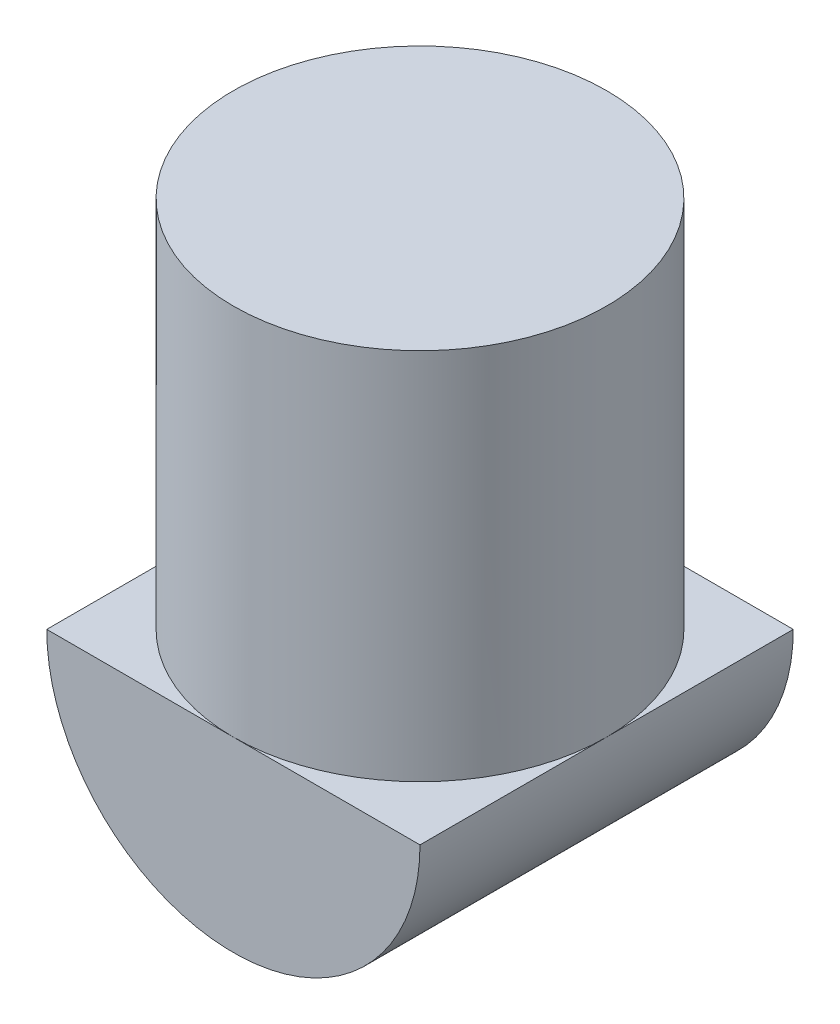
SolidWorks part; units mm, degrees
ref_plane "前视基准面" through (0, 0, 0) normal (0, 0, 1) x (1, 0, 0)
ref_plane "上视基准面" through (0, 0, 0) normal (0, 1, 0) x (1, 0, 0)
ref_plane "右视基准面" through (0, 0, 0) normal (1, 0, 0) x (0, 0, -1)
sketch "草图1" plane through (0, 0, 0) normal (0, 0, 1) x (1, 0, 0)
  line L0 (-61.9124, 0) -> (-8, 0) construction
  line L1 (0, 0) -> (0, 69.2952) construction
  line L4 (-8, 0) -> (-8, 16)
  line L5 (-8, 16) -> (8, 16)
  line L6 (8, 0) -> (8, 16)
  arc A0 (-8, 0) -> (8, 0) centre (0, 0) ccw
  dimension "D1" = 16
extrude "凸台-拉伸1" add sketch "草图1" along normal blind 16
sketch "草图2" plane through (0, 16, 0) normal (0, 1, 0) x (1, 0, 0)
  line L0 (0, 0) -> (0, -16) construction
  line L1 (8, -16) -> (-8, -16) construction
  line L3 (-9.694, 1.307) -> (9.1043, 1.307)
  line L4 (-9.694, 1.307) -> (-9.694, -16.9015)
  line L5 (-9.694, -16.9015) -> (9.1043, -16.9015)
  line L6 (9.1043, 1.307) -> (9.1043, -16.9015)
  circle A0 centre (0, -8) radius 8
extrude "切除-拉伸1" cut sketch "草图2" against normal blind 16
